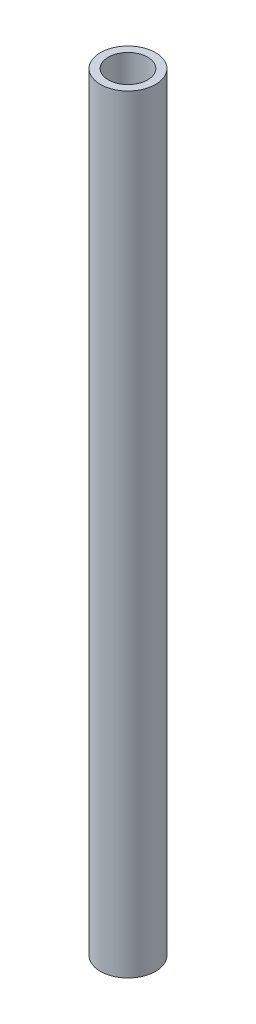
SolidWorks part; units mm, degrees
ref_plane "Front Plane" through (0, 0, 0) normal (0, 0, 1) x (1, 0, 0)
ref_plane "Top Plane" through (0, 0, 0) normal (0, 1, 0) x (1, 0, 0)
ref_plane "Right Plane" through (0, 0, 0) normal (1, 0, 0) x (0, 0, -1)
sketch "Sketch1" plane through (0, 0, 0) normal (0, 1, 0) x (1, 0, 0)
  circle A0 centre (0, 0) radius 7
  circle A1 centre (0, 0) radius 5
  dimension "D1" = 14
  dimension "D2" = 10
extrude "Boss-Extrude1" add sketch "Sketch1" along normal blind 195
